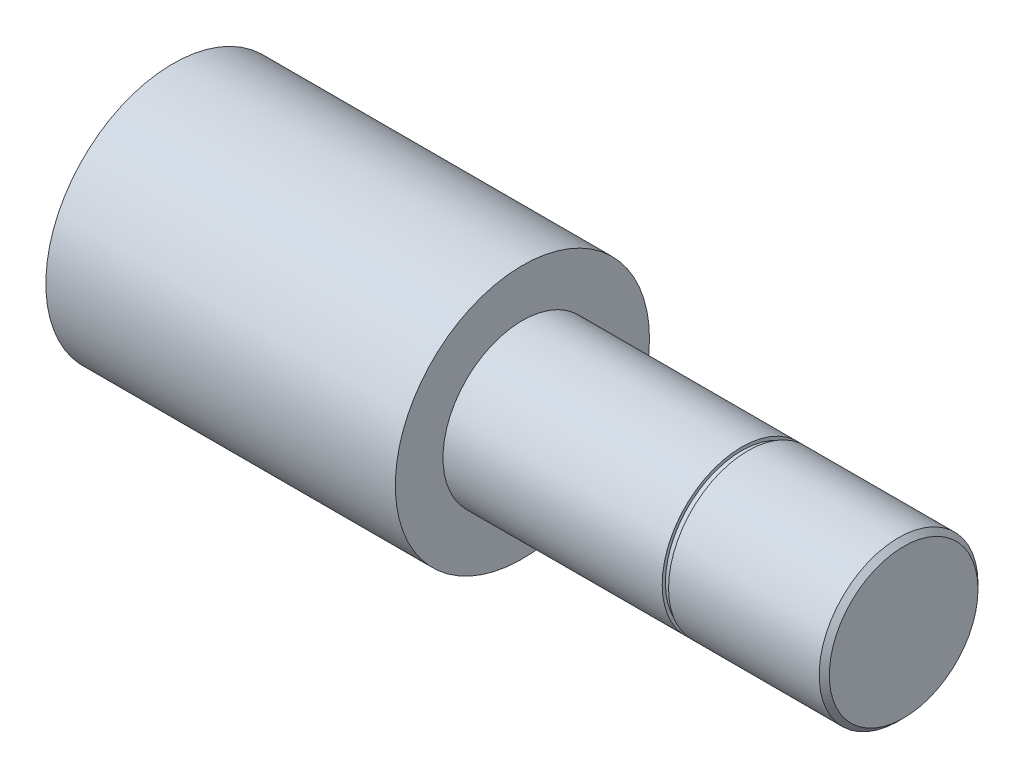
SolidWorks part; units mm, degrees
ref_plane "Ebene vorne" through (0, 0, 0) normal (0, 0, 1) x (1, 0, 0)
ref_plane "Ebene oben" through (0, 0, 0) normal (0, 1, 0) x (1, 0, 0)
ref_plane "Ebene rechts" through (0, 0, 0) normal (1, 0, 0) x (0, 0, -1)
sketch "Skizze1" plane through (0, 0, 0) normal (0, 0, 1) x (1, 0, 0)
  line L0 (0, 20) -> (0, 0)
  line L1 (0, 0) -> (115, 0)
  line L2 (115, 0) -> (115, 11.7)
  line L3 (115, 11.7) -> (114.2, 12.5)
  line L4 (114.2, 12.5) -> (55, 12.5)
  line L5 (55, 12.5) -> (55, 20)
  line L6 (55, 20) -> (0, 20)
  line L7 (0, 0) -> (115, 0) construction
revolve "Rotation1" add sketch "Skizze1" angle 360 about L7
sketch "Skizze2" plane through (0, 0, 0) normal (0, 0, 1) x (1, 0, 0)
  line L0 (89.5, 12.5) -> (89.5, 12)
  line L1 (89.5, 12) -> (90.5, 12)
  line L2 (90.5, 12) -> (90.5, 12.5)
  line L3 (90.5, 12.5) -> (89.5, 12.5)
  line L4 (115, -11.7) -> (115, 11.7) construction
  line L5 (114.2, 12.5) -> (55, 12.5) construction
  line L6 (79.8353, 0) -> (104.7383, 0) construction
  dimension "D1" = 25.5
  dimension "D2" = 1
  dimension "D3" = 0.5
  dimension "D4" = 0
revolve "Schnitt-Rotation1" cut sketch "Skizze2" angle 360 about L6
